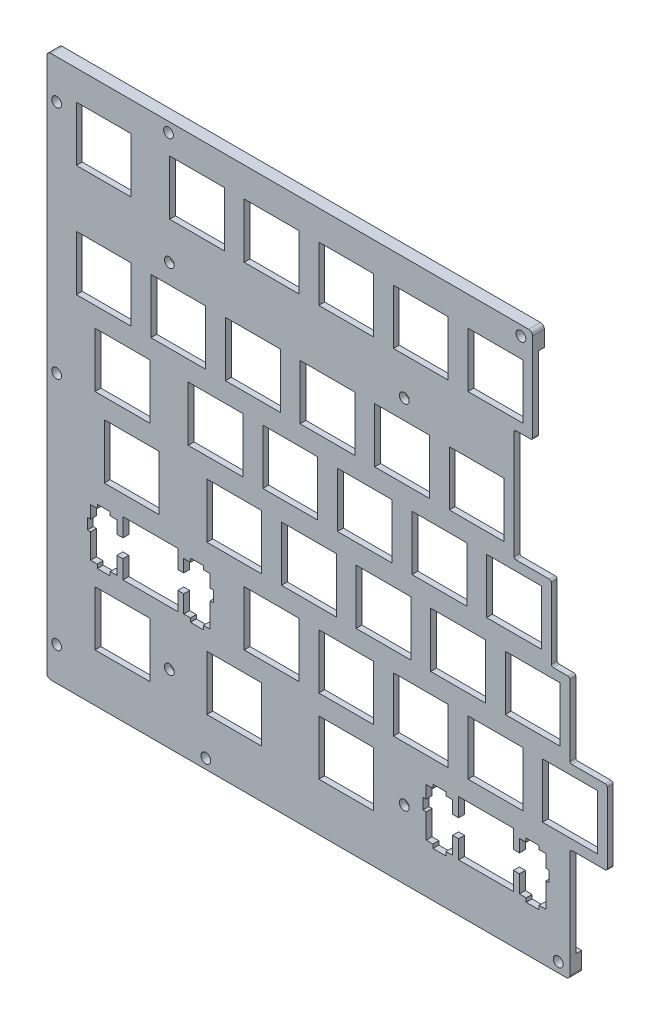
SolidWorks part; units mm, degrees
material "PC 高粘度"
ref_plane "前视基准面" through (0, 0, 0) normal (0, 0, 1) x (1, 0, 0)
ref_plane "上视基准面" through (0, 0, 0) normal (0, 1, 0) x (1, 0, 0)
ref_plane "右视基准面" through (0, 0, 0) normal (1, 0, 0) x (0, 0, -1)
other "Configuration Table"
sketch "Model" plane through (0, 0, 0) normal (0, 0, 1) x (1, 0, 0)
  line L0 (0.0951, 124.083) -> (119.158, 124.083)
  line L1 (138.208, 124.083) -> (138.208, 0.2577) construction
  line L2 (128.683, 0.2577) -> (0.0951, 0.2577)
  line L3 (0.0951, 0.2577) -> (0.0951, 124.083)
  line L4 (100.251, 16.7831) -> (100.251, 12.0826)
  line L5 (100.251, 12.0826) -> (98.7256, 12.0826)
  line L6 (98.7256, 12.0826) -> (98.7256, 15.3128)
  line L7 (98.7256, 15.3128) -> (97.0001, 15.3128)
  line L8 (97.0001, 15.3128) -> (97.0001, 16.2333)
  line L9 (97.0001, 16.2333) -> (93.701, 16.2333)
  line L10 (93.701, 16.2333) -> (93.701, 15.3128)
  line L11 (93.701, 15.3128) -> (91.9759, 15.3128)
  line L12 (91.9759, 15.3128) -> (91.9759, 12.0826)
  line L13 (91.9759, 12.0826) -> (91.1504, 12.0826)
  line L14 (91.1504, 12.0826) -> (91.1504, 9.2838)
  line L15 (91.1504, 9.2838) -> (91.9759, 9.2838)
  line L16 (91.9759, 9.2838) -> (91.9759, 3.0138)
  line L17 (91.9759, 3.0138) -> (93.701, 3.0138)
  line L18 (93.701, 3.0138) -> (93.701, 2.0326)
  line L19 (93.701, 2.0326) -> (97.0001, 2.0326)
  line L20 (97.0001, 2.0326) -> (97.0001, 3.0138)
  line L21 (97.0001, 3.0138) -> (98.7256, 3.0138)
  line L22 (98.7256, 3.0138) -> (98.7256, 7.4827)
  line L23 (98.7256, 7.4827) -> (100.251, 7.4827)
  line L24 (100.251, 7.4827) -> (100.251, 2.7836)
  line L25 (100.251, 2.7836) -> (114.25, 2.7836)
  line L26 (114.25, 2.7836) -> (114.25, 7.4827)
  line L27 (114.25, 7.4827) -> (115.776, 7.4827)
  line L28 (115.776, 7.4827) -> (115.776, 3.0138)
  line L29 (115.776, 3.0138) -> (117.5, 3.0138)
  line L30 (117.5, 3.0138) -> (117.5, 2.0326)
  line L31 (117.5, 2.0326) -> (120.8, 2.0326)
  line L32 (120.8, 2.0326) -> (120.8, 3.0138)
  line L33 (120.8, 3.0138) -> (122.525, 3.0138)
  line L34 (122.525, 3.0138) -> (122.525, 9.2838)
  line L35 (122.525, 9.2838) -> (123.351, 9.2838)
  line L36 (123.351, 9.2838) -> (123.351, 12.0826)
  line L37 (123.351, 12.0826) -> (122.525, 12.0826)
  line L38 (122.525, 12.0826) -> (122.525, 15.3128)
  line L39 (122.525, 15.3128) -> (120.8, 15.3128)
  line L40 (120.8, 15.3128) -> (120.8, 16.2333)
  line L41 (120.8, 16.2333) -> (117.5, 16.2333)
  line L42 (117.5, 16.2333) -> (117.5, 15.3128)
  line L43 (117.5, 15.3128) -> (115.776, 15.3128)
  line L44 (115.776, 15.3128) -> (115.776, 12.0826)
  line L45 (115.776, 12.0826) -> (114.25, 12.0826)
  line L46 (114.25, 12.0826) -> (114.25, 16.7831)
  line L47 (114.25, 16.7831) -> (100.251, 16.7831)
  line L48 (7.3822, 16.7831) -> (21.3817, 16.7831)
  line L49 (21.3817, 16.7831) -> (21.3817, 2.7836)
  line L50 (21.3817, 2.7836) -> (7.3822, 2.7836)
  line L51 (7.3822, 2.7836) -> (7.3822, 16.7831)
  line L52 (35.9572, 16.7831) -> (49.9565, 16.7831)
  line L53 (49.9565, 16.7831) -> (49.9565, 2.7836)
  line L54 (49.9565, 2.7836) -> (35.9572, 2.7836)
  line L55 (35.9572, 2.7836) -> (35.9572, 16.7831)
  line L56 (64.5322, 16.7831) -> (78.5315, 16.7831)
  line L57 (78.5315, 16.7831) -> (78.5315, 2.7836)
  line L58 (78.5315, 2.7836) -> (64.5322, 2.7836)
  line L59 (64.5322, 2.7836) -> (64.5322, 16.7831)
  line L60 (14.5259, 35.833) -> (14.5259, 31.1326)
  line L61 (14.5259, 31.1326) -> (13.0004, 31.1326)
  line L62 (13.0004, 31.1326) -> (13.0004, 34.3628)
  line L63 (13.0004, 34.3628) -> (11.2751, 34.3628)
  line L64 (11.2751, 34.3628) -> (11.2751, 35.2834)
  line L65 (11.2751, 35.2834) -> (7.9761, 35.2834)
  line L66 (7.9761, 35.2834) -> (7.9761, 34.3628)
  line L67 (7.9761, 34.3628) -> (6.2508, 34.3628)
  line L68 (6.2508, 34.3628) -> (6.2508, 31.1326)
  line L69 (6.2508, 31.1326) -> (5.4253, 31.1326)
  line L70 (5.4253, 31.1326) -> (5.4253, 28.3338)
  line L71 (5.4253, 28.3338) -> (6.2508, 28.3338)
  line L72 (6.2508, 28.3338) -> (6.2508, 22.0638)
  line L73 (6.2508, 22.0638) -> (7.9761, 22.0638)
  line L74 (7.9761, 22.0638) -> (7.9761, 21.0826)
  line L75 (7.9761, 21.0826) -> (11.2751, 21.0826)
  line L76 (11.2751, 21.0826) -> (11.2751, 22.0638)
  line L77 (11.2751, 22.0638) -> (13.0004, 22.0638)
  line L78 (13.0004, 22.0638) -> (13.0004, 26.5327)
  line L79 (13.0004, 26.5327) -> (14.5259, 26.5327)
  line L80 (14.5259, 26.5327) -> (14.5259, 21.8336)
  line L81 (14.5259, 21.8336) -> (28.5254, 21.8336)
  line L82 (28.5254, 21.8336) -> (28.5254, 26.5327)
  line L83 (28.5254, 26.5327) -> (30.0509, 26.5327)
  line L84 (30.0509, 26.5327) -> (30.0509, 22.0638)
  line L85 (30.0509, 22.0638) -> (31.7748, 22.0638)
  line L86 (31.7748, 22.0638) -> (31.7748, 21.0826)
  line L87 (31.7748, 21.0826) -> (35.0752, 21.0826)
  line L88 (35.0752, 21.0826) -> (35.0752, 22.0638)
  line L89 (35.0752, 22.0638) -> (36.8004, 22.0638)
  line L90 (36.8004, 22.0638) -> (36.8004, 28.3338)
  line L91 (36.8004, 28.3338) -> (37.6259, 28.3338)
  line L92 (37.6259, 28.3338) -> (37.6259, 31.1326)
  line L93 (37.6259, 31.1326) -> (36.8004, 31.1326)
  line L94 (36.8004, 31.1326) -> (36.8004, 34.3628)
  line L95 (36.8004, 34.3628) -> (35.0752, 34.3628)
  line L96 (35.0752, 34.3628) -> (35.0752, 35.2834)
  line L97 (35.0752, 35.2834) -> (31.7748, 35.2834)
  line L98 (31.7748, 35.2834) -> (31.7748, 34.3628)
  line L99 (31.7748, 34.3628) -> (30.0509, 34.3628)
  line L100 (30.0509, 34.3628) -> (30.0509, 31.1326)
  line L101 (30.0509, 31.1326) -> (28.5254, 31.1326)
  line L102 (28.5254, 31.1326) -> (28.5254, 35.833)
  line L103 (28.5254, 35.833) -> (14.5259, 35.833)
  line L104 (45.4822, 35.833) -> (59.4815, 35.833)
  line L105 (59.4815, 35.833) -> (59.4815, 21.8336)
  line L106 (59.4815, 21.8336) -> (45.4822, 21.8336)
  line L107 (45.4822, 21.8336) -> (45.4822, 35.833)
  line L108 (64.5322, 35.833) -> (78.5315, 35.833)
  line L109 (78.5315, 35.833) -> (78.5315, 21.8336)
  line L110 (78.5315, 21.8336) -> (64.5322, 21.8336)
  line L111 (64.5322, 21.8336) -> (64.5322, 35.833)
  line L112 (83.5822, 35.833) -> (97.5815, 35.833)
  line L113 (97.5815, 35.833) -> (97.5815, 21.8336)
  line L114 (97.5815, 21.8336) -> (83.5822, 21.8336)
  line L115 (83.5822, 21.8336) -> (83.5822, 35.833)
  line L116 (102.632, 35.833) -> (116.632, 35.833)
  line L117 (116.632, 35.833) -> (116.632, 21.8336)
  line L118 (116.632, 21.8336) -> (102.632, 21.8336)
  line L119 (102.632, 21.8336) -> (102.632, 35.833)
  line L120 (121.682, 35.833) -> (135.682, 35.833)
  line L121 (135.682, 35.833) -> (135.682, 21.8336)
  line L122 (135.682, 21.8336) -> (121.682, 21.8336)
  line L123 (121.682, 21.8336) -> (121.682, 35.833)
  line L124 (9.762, 54.8831) -> (23.7629, 54.8831)
  line L125 (23.7629, 54.8831) -> (23.7629, 40.8838)
  line L126 (23.7629, 40.8838) -> (9.762, 40.8838)
  line L127 (9.762, 40.8838) -> (9.762, 54.8831)
  line L128 (35.9572, 54.8831) -> (49.9565, 54.8831)
  line L129 (49.9565, 54.8831) -> (49.9565, 40.8838)
  line L130 (49.9565, 40.8838) -> (35.9572, 40.8838)
  line L131 (35.9572, 40.8838) -> (35.9572, 54.8831)
  line L132 (55.0072, 54.8831) -> (69.0065, 54.8831)
  line L133 (69.0065, 54.8831) -> (69.0065, 40.8838)
  line L134 (69.0065, 40.8838) -> (55.0072, 40.8838)
  line L135 (55.0072, 40.8838) -> (55.0072, 54.8831)
  line L136 (74.0572, 54.8831) -> (88.0565, 54.8831)
  line L137 (88.0565, 54.8831) -> (88.0565, 40.8838)
  line L138 (88.0565, 40.8838) -> (74.0572, 40.8838)
  line L139 (74.0572, 40.8838) -> (74.0572, 54.8831)
  line L140 (93.1072, 54.8831) -> (107.107, 54.8831)
  line L141 (107.107, 54.8831) -> (107.107, 40.8838)
  line L142 (107.107, 40.8838) -> (93.1072, 40.8838)
  line L143 (93.1072, 40.8838) -> (93.1072, 54.8831)
  line L144 (112.157, 54.8831) -> (126.157, 54.8831)
  line L145 (126.157, 54.8831) -> (126.157, 40.8838)
  line L146 (126.157, 40.8838) -> (112.157, 40.8838)
  line L147 (112.157, 40.8838) -> (112.157, 54.8831)
  line L148 (7.3822, 73.9331) -> (21.3817, 73.9331)
  line L149 (21.3817, 73.9331) -> (21.3817, 59.9338)
  line L150 (21.3817, 59.9338) -> (7.3822, 59.9338)
  line L151 (7.3822, 59.9338) -> (7.3822, 73.9331)
  line L152 (31.1947, 73.9331) -> (45.194, 73.9331)
  line L153 (45.194, 73.9331) -> (45.194, 59.9338)
  line L154 (45.194, 59.9338) -> (31.1947, 59.9338)
  line L155 (31.1947, 59.9338) -> (31.1947, 73.9331)
  line L156 (50.2447, 73.9331) -> (64.244, 73.9331)
  line L157 (64.244, 73.9331) -> (64.244, 59.9338)
  line L158 (64.244, 59.9338) -> (50.2447, 59.9338)
  line L159 (50.2447, 59.9338) -> (50.2447, 73.9331)
  line L160 (69.2947, 73.9331) -> (83.294, 73.9331)
  line L161 (83.294, 73.9331) -> (83.294, 59.9338)
  line L162 (83.294, 59.9338) -> (69.2947, 59.9338)
  line L163 (69.2947, 59.9338) -> (69.2947, 73.9331)
  line L164 (88.3447, 73.9331) -> (102.344, 73.9331)
  line L165 (102.344, 73.9331) -> (102.344, 59.9338)
  line L166 (102.344, 59.9338) -> (88.3447, 59.9338)
  line L167 (88.3447, 59.9338) -> (88.3447, 73.9331)
  line L168 (107.395, 73.9331) -> (121.394, 73.9331)
  line L169 (121.394, 73.9331) -> (121.394, 59.9338)
  line L170 (121.394, 59.9338) -> (107.395, 59.9338)
  line L171 (107.395, 59.9338) -> (107.395, 73.9331)
  line L172 (2.6197, 92.9831) -> (16.6192, 92.9831)
  line L173 (16.6192, 92.9831) -> (16.6192, 78.9838)
  line L174 (16.6192, 78.9838) -> (2.6197, 78.9838)
  line L175 (2.6197, 78.9838) -> (2.6197, 92.9831)
  line L176 (21.6697, 92.9831) -> (35.669, 92.9831)
  line L177 (35.669, 92.9831) -> (35.669, 78.9838)
  line L178 (35.669, 78.9838) -> (21.6697, 78.9838)
  line L179 (21.6697, 78.9838) -> (21.6697, 92.9831)
  line L180 (40.7197, 92.9831) -> (54.719, 92.9831)
  line L181 (54.719, 92.9831) -> (54.719, 78.9838)
  line L182 (54.719, 78.9838) -> (40.7197, 78.9838)
  line L183 (40.7197, 78.9838) -> (40.7197, 92.9831)
  line L184 (59.7697, 92.9831) -> (73.769, 92.9831)
  line L185 (73.769, 92.9831) -> (73.769, 78.9838)
  line L186 (73.769, 78.9838) -> (59.7697, 78.9838)
  line L187 (59.7697, 78.9838) -> (59.7697, 92.9831)
  line L188 (78.8197, 92.9831) -> (92.819, 92.9831)
  line L189 (92.819, 92.9831) -> (92.819, 78.9838)
  line L190 (92.819, 78.9838) -> (78.8197, 78.9838)
  line L191 (78.8197, 78.9838) -> (78.8197, 92.9831)
  line L192 (97.8683, 92.9831) -> (111.869, 92.9831)
  line L193 (111.869, 92.9831) -> (111.869, 78.9838)
  line L194 (111.869, 78.9838) -> (97.8683, 78.9838)
  line L195 (97.8683, 78.9838) -> (97.8683, 92.9831)
  line L196 (2.6197, 121.558) -> (16.6192, 121.558)
  line L197 (16.6192, 121.558) -> (16.6192, 107.559)
  line L198 (16.6192, 107.559) -> (2.6197, 107.559)
  line L199 (2.6197, 107.559) -> (2.6197, 121.558)
  line L200 (26.4322, 121.558) -> (40.4315, 121.558)
  line L201 (40.4315, 121.558) -> (40.4315, 107.559)
  line L202 (40.4315, 107.559) -> (26.4322, 107.559)
  line L203 (26.4322, 107.559) -> (26.4322, 121.558)
  line L204 (45.4822, 121.558) -> (59.4815, 121.558)
  line L205 (59.4815, 121.558) -> (59.4815, 107.559)
  line L206 (59.4815, 107.559) -> (45.4822, 107.559)
  line L207 (45.4822, 107.559) -> (45.4822, 121.558)
  line L208 (64.5322, 121.558) -> (78.5315, 121.558)
  line L209 (78.5315, 121.558) -> (78.5315, 107.559)
  line L210 (78.5315, 107.559) -> (64.5322, 107.559)
  line L211 (64.5322, 107.559) -> (64.5322, 121.558)
  line L212 (83.5822, 121.558) -> (97.5815, 121.558)
  line L213 (97.5815, 121.558) -> (97.5815, 107.559)
  line L214 (97.5815, 107.559) -> (83.5822, 107.559)
  line L215 (83.5822, 107.559) -> (83.5822, 121.558)
  line L216 (102.632, 121.558) -> (116.632, 121.558)
  line L217 (116.632, 121.558) -> (116.632, 107.559)
  line L218 (116.632, 107.559) -> (102.632, 107.559)
  line L219 (102.632, 107.559) -> (102.632, 121.558)
  line L233 (114.395, 76.453) -> (114.395, 105.033)
  line L234 (128.683, 19.303) -> (128.683, 0.2577)
  line L235 (114.395, 105.033) -> (119.158, 105.033)
  line L236 (119.158, 105.033) -> (119.158, 124.083)
  line L237 (114.395, 76.453) -> (123.92, 76.453)
  line L238 (123.92, 76.453) -> (123.92, 57.403)
  line L239 (123.92, 57.403) -> (128.683, 57.403)
  line L240 (128.683, 57.403) -> (128.683, 38.353)
  line L241 (128.683, 38.353) -> (138.208, 38.353)
  line L242 (138.208, 38.353) -> (138.208, 19.303)
  line L243 (138.208, 19.303) -> (128.683, 19.303)
  dimension "D1" = 19.05
  dimension "D2" = 4.763
  dimension "D3" = 28.58
  dimension "D4" = 9.525
extrude "凸台-拉伸1" add sketch "Model" along normal blind 1.5
sketch "草图5" plane through (0, 0.2577, 0) normal (0, -1, 0) x (1, 0, 0)
  line L4 (0.0951, 0) -> (128.683, 0)
  line L5 (128.683, 0) -> (128.683, 1.5)
  line L6 (128.683, 1.5) -> (0.0951, 1.5)
  line L7 (0.0951, 1.5) -> (0.0951, 0)
  line L8 (0.0951, 0) -> (128.683, 0)
  line L9 (128.683, 0) -> (128.683, 1.5)
  line L10 (128.683, 1.5) -> (0.0951, 1.5)
  line L11 (0.0951, 1.5) -> (0.0951, 0)
  dimension "D1" = 0
extrude "凸台-拉伸3" add sketch "草图5" along normal blind 4.76
sketch "草图2" plane through (0, 0, 1.5) normal (0, 0, 1) x (1, 0, 0)
  line L11 (119.158, 124.083) -> (0.0951, 124.083) construction
  line L12 (0.0951, 124.083) -> (0.0951, -4.5023) construction
  line L13 (128.683, -4.5023) -> (0.0951, -4.5023) construction
  line L14 (119.158, 124.083) -> (0.0951, 124.083)
  line L15 (0.0951, 124.083) -> (0.0951, -4.5023)
  line L16 (128.683, -4.5023) -> (0.0951, -4.5023)
  line L17 (119.158, 129.083) -> (-4.9049, 129.083)
  line L18 (-4.9049, 129.083) -> (-4.9049, -9.5023)
  line L19 (128.683, -9.5023) -> (-4.9049, -9.5023)
  line L20 (119.158, 124.083) -> (119.158, 129.083)
  line L21 (128.683, -9.5023) -> (128.683, -4.5023)
  dimension "D1" = 5
extrude "凸台-拉伸2" add sketch "草图2" against normal blind 3
sketch "草图3" plane through (0, 0, 1.5) normal (0, 0, 1) x (1, 0, 0)
  line L0 (119.158, 105.033) -> (119.158, 129.083) construction
  line L2 (128.683, -9.5023) -> (128.683, 19.303) construction
  line L4 (-4.9049, -9.5023) -> (128.683, -9.5023) construction
  line L5 (119.158, 129.083) -> (-4.9049, 129.083) construction
  circle A0 centre (125.683, -7.0023) radius 1.25
  circle A1 centre (116.158, 126.583) radius 1.25
  dimension "D1" = 2.5
  dimension "D2" = 3
  dimension "D3" = 2.5
  dimension "D4" = 3
  dimension "D5" = 2.5
extrude "切除-拉伸1" cut sketch "草图3" against normal blind 3
pattern_linear "阵列(线性)1" count 2 spacing 90 along (-1, 0, 0) of "切除-拉伸1"
sketch "草图4" plane through (0, 0, 1.5) normal (0, 0, 1) x (1, 0, 0)
  line L2 (-4.9049, 129.083) -> (-4.9049, -9.5023) construction
  line L3 (119.158, 129.083) -> (-4.9049, 129.083) construction
  circle A0 centre (-2.4049, 119.083) radius 1.25
  dimension "D1" = 2.5
  dimension "D2" = 2.5
  dimension "D3" = 10
extrude "切除-拉伸2" cut sketch "草图4" against normal blind 3
pattern_linear "阵列(线性)2" count 3 spacing 60 along (0, -1, 0) of "切除-拉伸2"
fillet "圆角1" radius 1 4 edges at (-4.9049, -9.5023, 0) (128.683, -9.5023, 0) (119.158, 129.083, 0) (-4.9049, 129.083, 0)
fillet "圆角2" radius 0.5 10 edges at (119.158, 105.033, 0.75) (114.395, 105.033, 0.75) (123.92, 76.453, 0.75) (114.395, 76.453, 0.75) (128.683, 57.403, 0.75) (123.92, 57.403, 0.75) (138.208, 38.353, 0.75) (128.683, 38.353, 0.75) (138.208, 19.303, 0.75) (128.683, 19.303, 0.75)
sketch "草图6" plane through (0, 0, 1.5) normal (0, 0, 1) x (1, 0, 0)
  line L0 (54.719, 92.9831) -> (40.7197, 92.9831) construction
  line L1 (26.3817, 97.9831) -> (86.3817, 97.9831) construction
  line L2 (26.3817, 97.9831) -> (26.3817, 7.9831) construction
  line L3 (26.3817, 7.9831) -> (86.3817, 7.9831) construction
  line L4 (86.3817, 97.9831) -> (86.3817, 7.9831) construction
  line L5 (21.3817, 2.7836) -> (21.3817, 16.7831) construction
  circle A3 centre (26.3817, 7.9831) radius 1.25
  circle A4 centre (86.3817, 7.9831) radius 1.25
  circle A5 centre (86.3817, 97.9831) radius 1.25
  circle A6 centre (26.3817, 97.9831) radius 1.25
  dimension "D1" = 60
  dimension "D5" = 2.5
  dimension "D2" = 90
  dimension "D3" = 5
  dimension "D4" = 5
extrude "切除-拉伸3" cut sketch "草图6" against normal blind 10
